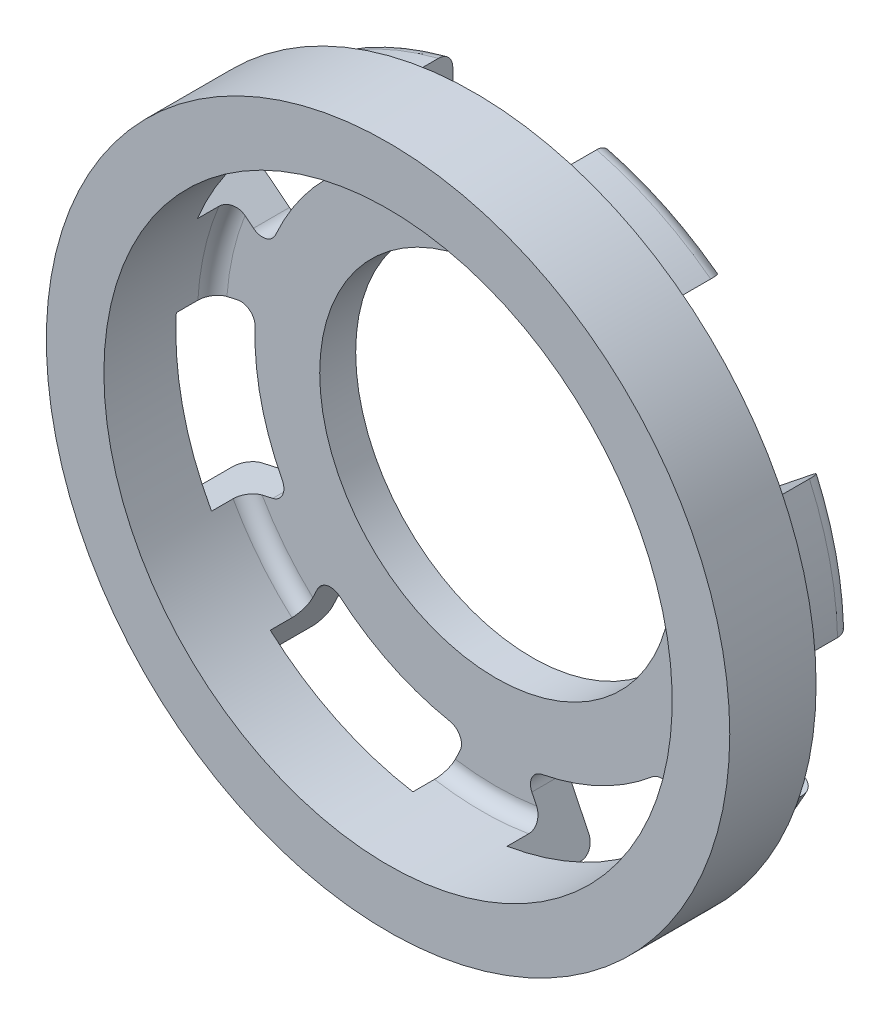
SolidWorks part; units mm, degrees
ref_plane "Front Plane" through (0, 0, 0) normal (0, 0, 1) x (1, 0, 0)
ref_plane "Top Plane" through (0, 0, 0) normal (0, 1, 0) x (1, 0, 0)
ref_plane "Right Plane" through (0, 0, 0) normal (1, 0, 0) x (0, 0, -1)
sketch "Croquis1" plane through (0, 0, 0) normal (0, 0, 1) x (1, 0, 0)
  circle A0 centre (0, 0) radius 23.75
  dimension "D1" = 47.5
extrude "Saliente-Extruir1" add sketch "Croquis1" along normal blind 6
sketch "Croquis4" plane through (0, 0, 0) normal (0, 0, -1) x (-1, 0, 0)
  circle A0 centre (0, 0) radius 22.25
  circle A1 centre (0, 0) radius 23.75 construction
  dimension "D1" = 1.5
extrude "Cortar-Extruir1" cut sketch "Croquis4" against normal blind 1
sketch "Croquis5" plane through (0, 0, 1) normal (0, 0, -1) x (-1, 0, 0)
  circle A0 centre (0, 0) radius 19.75
  circle A1 centre (0, 0) radius 23.75 construction
  dimension "D1" = 4
extrude "Cortar-Extruir2" cut sketch "Croquis5" against normal through all both and the other way through all
sketch "Croquis6" plane through (0, 0, 1) normal (0, 0, -1) x (-1, 0, 0)
  circle A1 centre (0, 0) radius 22.25
  circle A2 centre (0, 0) radius 22.25
  dimension "D1" = 0
extrude "Saliente-Extruir2" add sketch "Croquis6" along normal blind 5
sketch "Croquis7" plane through (0, 0, 1) normal (0, 0, 1) x (1, 0, 0)
  circle A1 centre (0, 0) radius 19.75
  circle A2 centre (0, 0) radius 19.75
  dimension "D1" = 0
extrude "Cortar-Extruir3" cut sketch "Croquis7" against normal blind 2.5
fillet "Redondeo1" radius 1 1 edges at (19.75, 0, -1.5)
sketch "Croquis8" plane through (0, 0, -4) normal (0, 0, -1) x (-1, 0, 0)
  line L0 (0, 22.25) -> (0, -22.25) construction
  line L1 (-5.5, 21.5595) -> (-5.5, 15.8213)
  line L2 (5.5, 21.5595) -> (5.5, 15.8213)
  line L5 (-5.5, 22.25) -> (-5.5, -22.25) construction
  line L7 (5.5, 22.25) -> (5.5, -22.25) construction
  arc A0 (5.5, 15.8213) -> (-5.5, 15.8213) centre (0, 0) ccw
  circle A1 centre (0, 0) radius 22.25 construction
  circle A2 centre (0, 0) radius 22.25 construction
  arc A3 (5.5, 21.5595) -> (-5.5, 21.5595) centre (0, 0) ccw
  dimension "D1" = 33.5
  dimension "D2" = 5.5
  dimension "D3" = 5.5
extrude "Cortar-Extruir4" cut sketch "Croquis8" against normal blind 2.5
sketch "Croquis9" plane through (0, 0, -1.5) normal (0, 0, -1) x (-1, 0, 0)
  line L2 (5.5, 17.9252) -> (5.5, 21.5595)
  line L3 (-5.5, 21.5595) -> (-5.5, 17.9252)
  line L4 (5.5, 17.9252) -> (5.5, 21.5595)
  line L5 (-5.5, 21.5595) -> (-5.5, 17.9252)
  arc A2 (5.5, 21.5595) -> (-5.5, 21.5595) centre (0, 0) ccw
  arc A3 (5.5, 17.9252) -> (-5.5, 17.9252) centre (0, 0) ccw
  arc A4 (5.5, 21.5595) -> (-5.5, 21.5595) centre (0, 0) ccw
  arc A5 (5.5, 17.9252) -> (-5.5, 17.9252) centre (0, 0) ccw
  dimension "D1" = 0
extrude "Cortar-Extruir5" cut sketch "Croquis9" against normal blind 2.5
pattern_circular "MatrizC1" count 7 over 360 about axis through (0, 0, 0) along (0, 0, 1) of "Cortar-Extruir5", "Cortar-Extruir4"
fillet "Redondeo2" radius 1 14 edges at (14.2007, -8.8827, -2.75) (16.6485, 1.8415, -2.75) (11.8199, -11.8681, -2.75) (1.9093, -16.6408, -2.75) (-1.9093, -16.6408, -2.75) (-11.8199, -11.8681, -2.75) (-14.2007, -8.8827, -2.75) (-16.6485, 1.8415, -2.75) (-15.7988, 5.5643, -2.75) (-8.9404, 14.1645, -2.75) (-5.5, 15.8213, -2.75) (5.5, 15.8213, -2.75) (8.9404, 14.1645, -2.75) (15.7988, 5.5643, -2.75)
fillet "Redondeo3" radius 1 7 edges at (-21.6921, 4.9511, -4) (-9.6539, 20.0466, -4) (9.6539, 20.0466, -4) (21.6921, 4.9511, -4) (17.3958, -13.8726, -4) (0, -22.25, -4) (-17.3958, -13.8726, -4)
sketch "Croquis10" plane through (0, 0, -4) normal (0, 0, -1) x (-1, 0, 0)
  circle A0 centre (0, 0) radius 12.25
  dimension "D1" = 24.5
extrude "Cortar-Extruir6" cut sketch "Croquis10" against normal through all both and the other way through all
